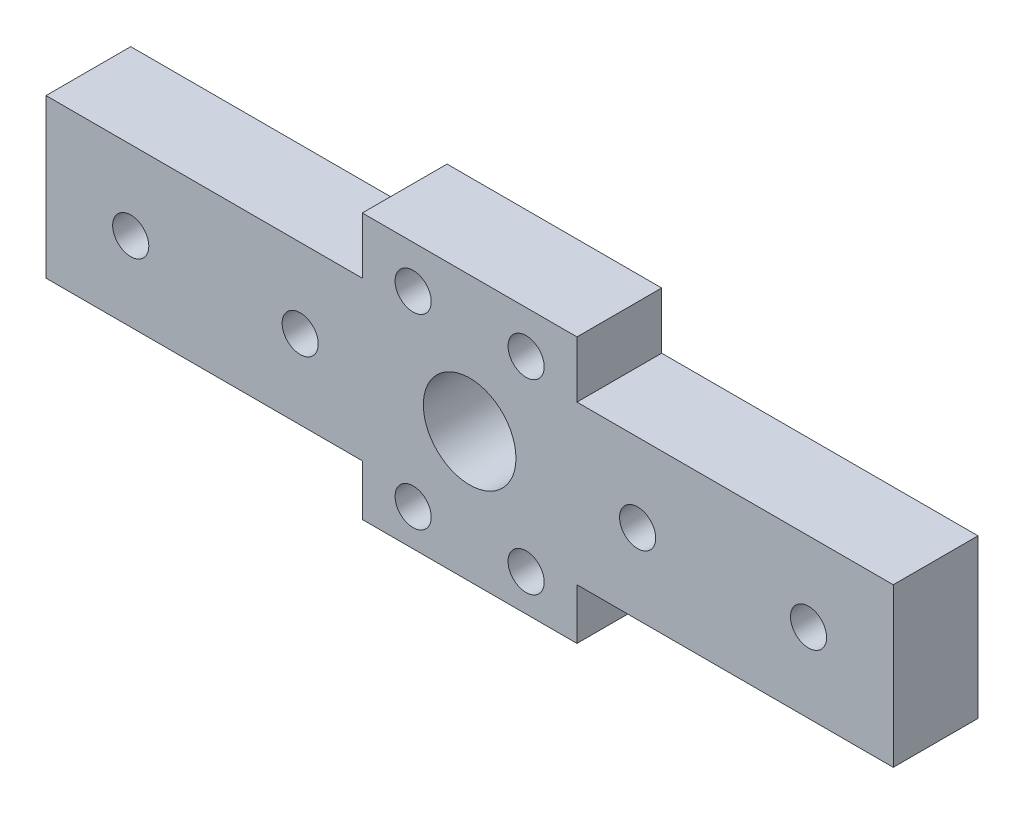
SolidWorks part; units mm, degrees
ref_plane "前视基准面" through (0, 0, 0) normal (0, 0, 1) x (1, 0, 0)
ref_plane "上视基准面" through (0, 0, 0) normal (0, 1, 0) x (1, 0, 0)
ref_plane "右视基准面" through (0, 0, 0) normal (1, 0, 0) x (0, 0, -1)
sketch "草图1" plane through (0, 0, 0) normal (0, 0, 1) x (1, 0, 0)
  line L0 (0, 11.5) -> (9.1, 11.5) construction
  line L1 (37.5, 34.267) -> (37.5, 15.6) construction
  line L2 (0, 11.5) -> (0, 4.5)
  line L3 (65.9, 11.5) -> (75, 11.5) construction
  line L4 (75, 4.5) -> (75, 18.5)
  line L5 (75, 11.5) -> (69.1, 11.5) construction
  line L6 (75, 18.5) -> (47, 18.5)
  line L7 (47, 18.5) -> (47, 23.5)
  line L8 (47, 23.5) -> (28, 23.5)
  line L9 (28, 23.5) -> (28, 18.5)
  line L10 (28, 18.5) -> (0, 18.5)
  line L11 (5.9, 11.5) -> (0, 11.5) construction
  line L12 (0, 18.5) -> (0, 11.5)
  line L13 (28, 0) -> (47, 0)
  line L15 (20.1, 11.5) -> (20.9, 11.5) construction
  line L16 (75, 4.5) -> (47, 4.5)
  line L17 (47, 4.5) -> (47, 0)
  line L18 (37.5, 7.4) -> (37.5, 0) construction
  line L19 (28, 4.5) -> (28, 0)
  line L20 (28, 4.5) -> (0.4162, 4.5)
  line L21 (0.4162, 4.5) -> (0, 4.5)
  circle A0 centre (37.5, 11.5) radius 4.1
  circle A5 centre (67.5, 11.5) radius 1.6
  circle A6 centre (32.5, 3.2278) radius 1.6
  circle A7 centre (42.5, 3.25) radius 1.6
  circle A8 centre (42.5, 19.75) radius 1.6
  circle A9 centre (32.5, 19.75) radius 1.6
  circle A10 centre (7.5, 11.5) radius 1.6
  circle A11 centre (52.3705, 11.554) radius 1.6
  circle A12 centre (22.5, 11.5) radius 1.6
extrude "凸台-拉伸1" add sketch "草图1" along normal blind 7.5
